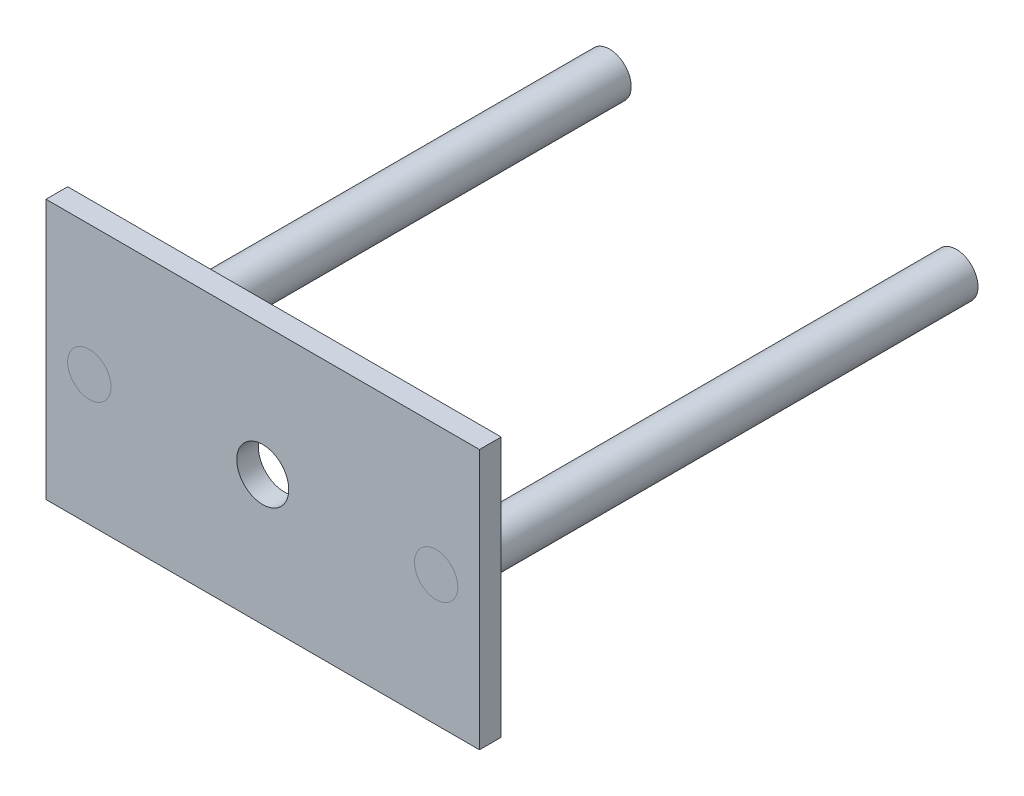
SolidWorks part; units mm, degrees
ref_plane "Front Plane" through (0, 0, 0) normal (0, 0, 1) x (1, 0, 0)
ref_plane "Top Plane" through (0, 0, 0) normal (0, 1, 0) x (1, 0, 0)
ref_plane "Right Plane" through (0, 0, 0) normal (1, 0, 0) x (0, 0, -1)
sketch "Sketch1" plane through (0, 0, 0) normal (0, 0, 1) x (1, 0, 0)
  line L1 (-50, -30) -> (50, -30)
  line L2 (-50, -30) -> (-50, 30)
  line L3 (-50, 30) -> (50, 30)
  line L4 (50, -30) -> (50, 30)
  line L5 (-50, -30) -> (50, 30) construction
  line L6 (-50, 30) -> (50, -30) construction
  circle A0 centre (0, 0) radius 6
  circle A1 centre (-40, 0) radius 5
  circle A2 centre (40, 0) radius 5
  dimension "D1" = 12
  dimension "D2" = 80
  dimension "D3" = 10
  dimension "D4" = 40
  dimension "D5" = 100
  dimension "D6" = 60
extrude "Boss-Extrude1" add sketch "Sketch1" along normal blind 5
sketch "Sketch2" plane through (0, 0, 5) normal (0, 0, 1) x (1, 0, 0)
  circle A0 centre (40, 0) radius 5 construction
  circle A1 centre (-40, 0) radius 5 construction
  circle A2 centre (40, 0) radius 5
  circle A3 centre (-40, 0) radius 5
extrude "Boss-Extrude2" add sketch "Sketch2" against normal blind 120 separate body
